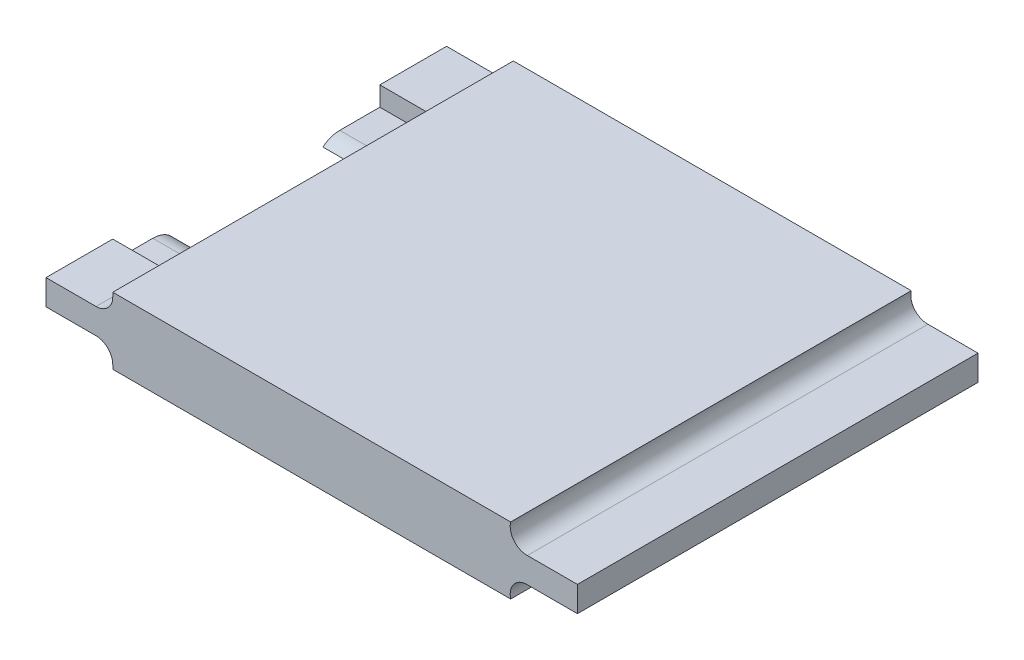
SolidWorks part; units mm, degrees
material "ABS"
ref_plane "정면" through (0, 0, 0) normal (0, 0, 1) x (1, 0, 0)
ref_plane "윗면" through (0, 0, 0) normal (0, 1, 0) x (1, 0, 0)
ref_plane "우측면" through (0, 0, 0) normal (1, 0, 0) x (0, 0, -1)
sketch "스케치1" plane through (0, 0, 0) normal (0, 0, 1) x (1, 0, 0)
  line L0 (0, 0) -> (0, 10)
  line L1 (29.8, 10) -> (-29.8, 10)
  line L2 (-32.3, 6.9) -> (-39.8, 6.9)
  line L3 (-39.8, 6.9) -> (-39.8, 3.1)
  line L4 (-39.8, 3.1) -> (-32.3, 3.1)
  line L5 (-29.8, 0) -> (29.8, 0)
  line L6 (39.8, 3.1) -> (32.3, 3.1)
  line L7 (39.8, 6.9) -> (39.8, 3.1)
  line L8 (32.3, 6.9) -> (39.8, 6.9)
  line L9 (-29.8, 10) -> (-29.8, 9.4)
  line L10 (-29.8, 0.6) -> (-29.8, 0)
  arc A2 (32.3, 3.1) -> (29.8, 0) centre (32.2267, 0.6011) ccw
  arc A3 (29.8, 10) -> (32.3, 6.9) centre (32.2267, 9.3989) ccw
  arc A5 (-32.3, 3.1) -> (-29.8, 0.6) centre (-32.3, 0.6) cw
  arc A6 (-29.8, 9.4) -> (-32.3, 6.9) centre (-32.3, 9.4) cw
  point P13 (0, 5)
  point P14 (-39.8, 5)
  point P15 (0, 0)
  dimension "D5" = 2.5
  dimension "D6" = 2.5
  dimension "D1" = 39.8
  dimension "D2" = 29.8
  dimension "D3" = 10
  dimension "D4" = 29.8
  dimension "D7" = 3.8
extrude "보스-돌출1" add sketch "스케치1" along normal blind 60
sketch "스케치2" plane through (-39.8, 0, 0) normal (-1, 0, 0) x (0, 0, 1)
  line L1 (44, 4) -> (50, 4)
  line L2 (50, 4) -> (50, 8)
  line L3 (16, 4) -> (10, 4)
  line L4 (50, 8) -> (10, 8)
  line L5 (30, 8) -> (30, 0)
  line L6 (20, 0) -> (40, 0)
  line L7 (60, 6.9) -> (60, 3.1) construction
  line L8 (10, 4) -> (10, 8)
  line L9 (60, 0) -> (0, 0) construction
  arc A0 (40, 0) -> (44, 4) centre (44, 0) cw
  arc A1 (20, 0) -> (16, 4) centre (16, 0) ccw
  line M12 (0, 3.1) -> (60, 3.1)
  line M14 (60, 6.9) -> (0, 6.9)
  dimension "D4" = 4
  dimension "D1" = 4
  dimension "D2" = 4
  dimension "D3" = 10
  dimension "D5" = 20
  dimension "D6" = 10
extrude "컷-돌출1" cut sketch "스케치2" against normal blind 17.3 contours A1 L5 L8 L3 M12 M14 | L6 A0 L5 M12 | A0 L1 L2 L5 M12 M14
